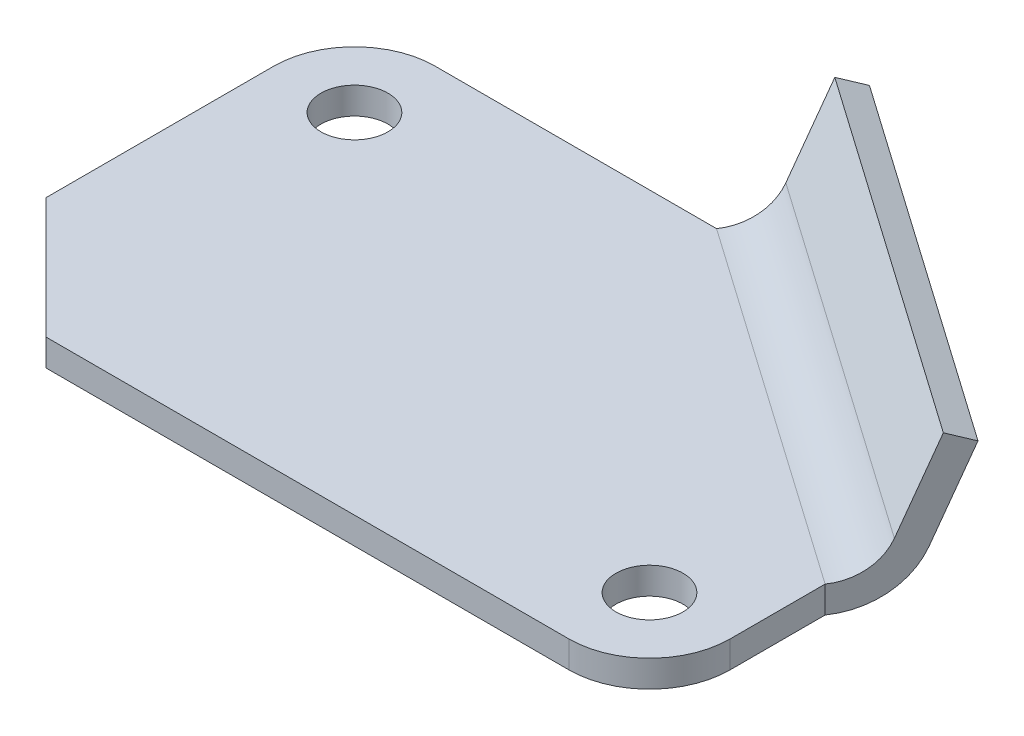
SolidWorks part; units mm, degrees
material "Manganese Bronze"
ref_plane "Front Plane" through (0, 0, 0) normal (0, 0, 1) x (1, 0, 0)
ref_plane "Top Plane" through (0, 0, 0) normal (0, 1, 0) x (1, 0, 0)
ref_plane "Right Plane" through (0, 0, 0) normal (1, 0, 0) x (0, 0, -1)
sketch "Sketch1" plane through (0, 0, 0) normal (0, 1, 0) x (1, 0, 0)
  line L0 (-12, 0) -> (-12, -34)
  line L1 (-12, -34) -> (6, -52)
  line L2 (6, -52) -> (84, -52)
  line L3 (96, -40) -> (96, -25.8112)
  line L4 (96, -25.8112) -> (42, 12)
  line L5 (42, 12) -> (0, 12)
  circle A0 centre (0, 0) radius 5
  circle A1 centre (84, -40) radius 5
  arc A2 (84, -52) -> (96, -40) centre (84, -40) ccw
  arc A3 (0, 12) -> (-12, 0) centre (0, 0) ccw
  point P15 (-12, 12)
  dimension "D1" = 10
  dimension "D2" = 10
  dimension "D9" = 12
  dimension "D3" = 18
  dimension "D4" = 18
  dimension "D5" = 54
  dimension "D6" = 108
  dimension "D7" = 35
  dimension "D8" = 64
extrude "Boss-Extrude1" add sketch "Sketch1" along normal blind 4
ref_plane "Plane2" through (76.5443, 0, 53.5969) normal (0.8192, 0, 0.5736) x (0, -1, 0)
sketch "Sketch3" plane through (76.5443, 0, 53.5969) normal (0.8192, 0, 0.5736) x (0, -1, 0)
  line L0 (-20.4853, 50.2907) -> (-21.9837, 46.582)
  line L1 (-21.9837, 46.582) -> (-9.0031, 41.3375)
  line L2 (-20.4853, 50.2907) -> (-7.5047, 45.0462)
  line L3 (-4, 33.92) -> (0, 33.92)
  line L4 (-4, 22.2973) -> (-4, 33.92) construction
  arc A0 (-9.0031, 41.3375) -> (-4, 33.92) centre (-12, 33.92) cw
  arc A1 (-7.5047, 45.0462) -> (0, 33.92) centre (-12, 33.92) cw
  point P2 (-58.5243, 84.6551)
  point P12 (0, 0)
  point P13 (-24.0431, 53.468)
  point P14 (-24.789, 51.6105)
  point P15 (0, 0)
  dimension "D1" = 112
  dimension "D4" = 12
  dimension "D2" = 4
  dimension "D3" = 14
extrude "Boss-Extrude2" add sketch "Sketch3" against normal up to vertex (65.9218 mm away)
